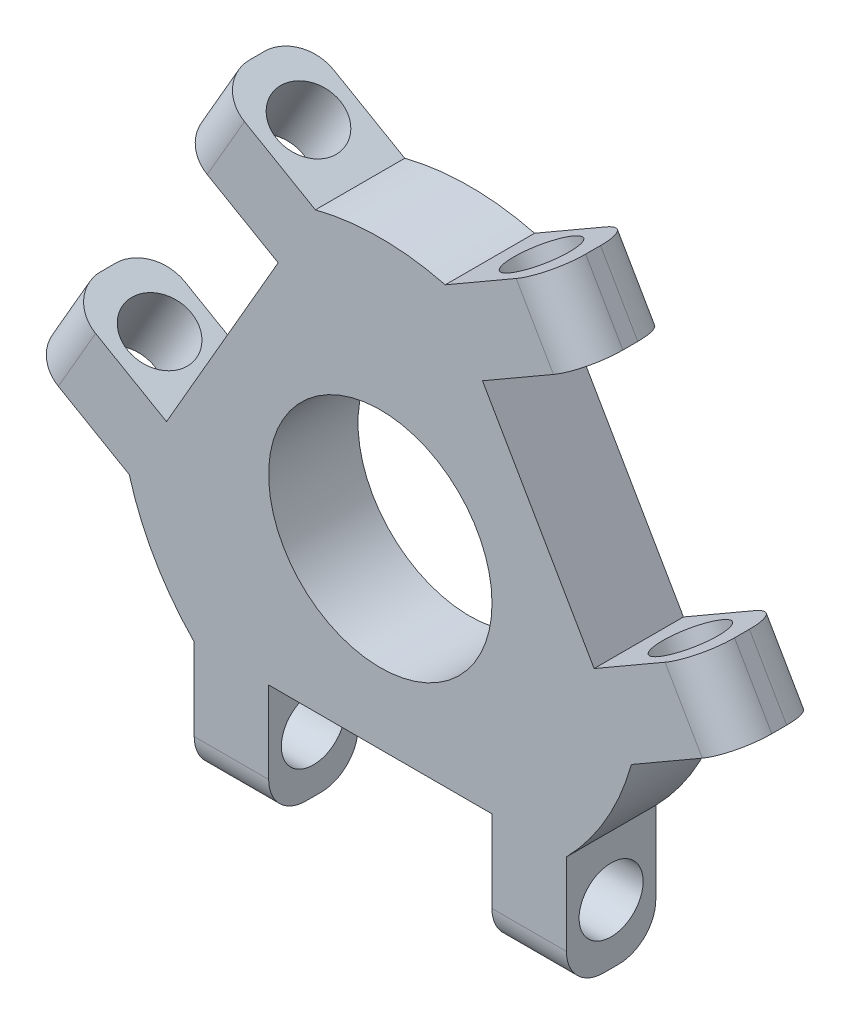
SolidWorks part; units mm, degrees
ref_plane "Front Plane" through (0, 0, 0) normal (0, 0, 1) x (1, 0, 0)
ref_plane "Top Plane" through (0, 0, 0) normal (0, 1, 0) x (1, 0, 0)
ref_plane "Right Plane" through (0, 0, 0) normal (1, 0, 0) x (0, 0, -1)
sketch "Sketch1" plane through (0, 0, 0) normal (0, 0, 1) x (1, 0, 0)
  line L1 (-8.7201, 33.8963) -> (-33.7151, -9.3963)
  line L2 (-24.995, -24.5) -> (24.995, -24.5)
  line L3 (33.7151, -9.3963) -> (8.7201, 33.8963)
  arc A0 (-33.7151, -9.3963) -> (-24.995, -24.5) centre (0, 0) ccw
  circle A1 centre (0, 0) radius 15
  circle A2 centre (0, 0) radius 24.5 construction
  arc A3 (8.7201, 33.8963) -> (-8.7201, 33.8963) centre (0, 0) ccw
  arc A4 (24.995, -24.5) -> (33.7151, -9.3963) centre (0, 0) ccw
  dimension "D1" = 70
  dimension "D2" = 30
  dimension "D3" = 49
extrude "Boss-Extrude1" add sketch "Sketch1" along normal blind 12
sketch "Sketch2" plane through (0, 0, 0) normal (0, 0, -1) x (-1, 0, 0)
  line L0 (33.7151, -9.3963) -> (47.5715, -1.3963)
  line L1 (8.7201, 33.8963) -> (33.7151, -9.3963) construction
  line L2 (47.5715, -1.3963) -> (42.5715, 7.2639)
  line L3 (42.5715, 7.2639) -> (28.7151, -0.7361)
  line L4 (28.7151, -0.7361) -> (33.7151, -9.3963)
  line L5 (0, 0) -> (42.5715, 24.5787) construction
  line L6 (13.7201, 25.2361) -> (8.7201, 33.8963)
  line L7 (27.5765, 33.2361) -> (13.7201, 25.2361)
  line L8 (22.5765, 41.8963) -> (27.5765, 33.2361)
  line L9 (8.7201, 33.8963) -> (22.5765, 41.8963)
  dimension "D1" = 90
  dimension "D2" = 16
  dimension "D3" = 10
extrude "Boss-Extrude2" add sketch "Sketch2" against normal blind 12
sketch "Sketch3" plane through (-12.4975, -21.6463, 0) normal (-0.5, -0.866, 0) x (0.866, -0.5, 0)
  line L0 (-40.5, 12) -> (-40.5, 0) construction
  line L1 (-24.5, 12) -> (-40.5, 12) construction
  circle A0 centre (-32.5, 6) radius 4.3
  point P2 (0, 0)
  point P5 (-40.5, 6)
  point P6 (0, 0)
  point P9 (-32.5, 12)
  dimension "D1" = 8.6
extrude "Cut-Extrude1" cut sketch "Sketch3" against normal through all
fillet "Fillet1" radius 5 4 edges at (-25.0765, 37.5662, 0) (-25.0765, 37.5662, 12) (-45.0715, 2.9338, 0) (-45.0715, 2.9338, 12)
pattern_circular "CirPattern1" count 3 over 360 about axis through (0, 0, 0) along (0, 0, 1) of "Fillet1", "Cut-Extrude1", "Boss-Extrude2"
